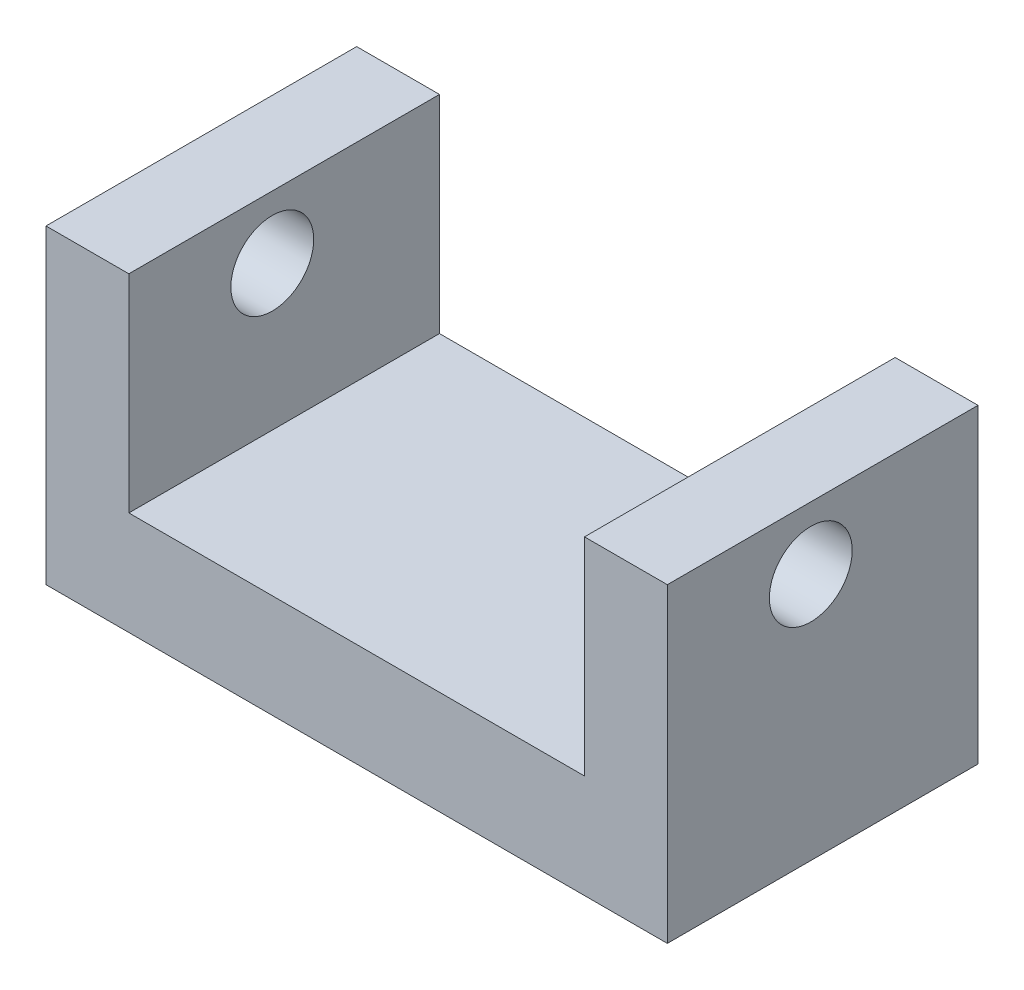
SolidWorks part; units mm, degrees
ref_plane "前视基准面" through (0, 0, 0) normal (0, 0, 1) x (1, 0, 0)
ref_plane "上视基准面" through (0, 0, 0) normal (0, 1, 0) x (1, 0, 0)
ref_plane "右视基准面" through (0, 0, 0) normal (1, 0, 0) x (0, 0, -1)
sketch "Sketch1" plane through (0, 0, 0) normal (0, 0, 1) x (1, 0, 0)
  line L0 (0, 0) -> (0, 75)
  line L1 (0, 75) -> (20, 75)
  line L2 (20, 75) -> (20, 25)
  line L3 (20, 25) -> (130, 25)
  line L4 (130, 25) -> (130, 75)
  line L5 (130, 75) -> (150, 75)
  line L6 (150, 75) -> (150, 0)
  line L7 (150, 0) -> (0, 0)
  dimension "D1" = 150
  dimension "D2" = 75
  dimension "D3" = 75
  dimension "D4" = 20
  dimension "D5" = 20
  dimension "D6" = 50
extrude "Boss-Extrude1" add sketch "Sketch1" along normal blind 75
sketch "Sketch2" plane through (150, 0, 0) normal (1, 0, 0) x (0, 0, -1)
  circle A0 centre (-40.3687, 59.8871) radius 10
  dimension "D1" = 20
extrude "Cut-Extrude1" cut sketch "Sketch2" against normal through all
